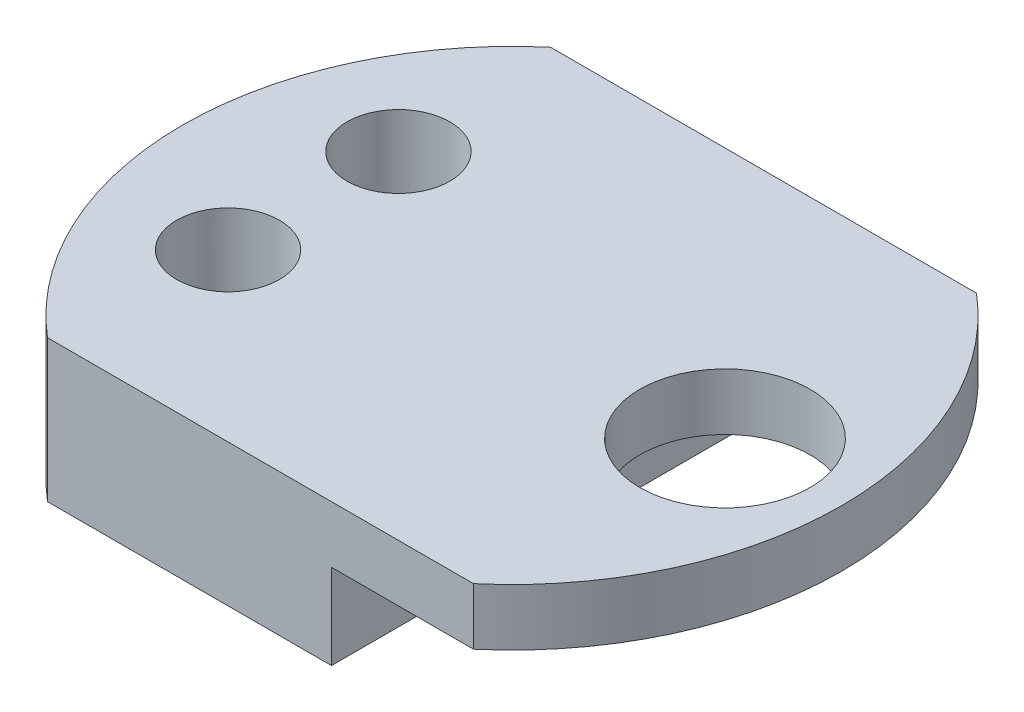
SolidWorks part; units mm, degrees
ref_plane "Front Plane" through (0, 0, 0) normal (0, 0, 1) x (1, 0, 0)
ref_plane "Top Plane" through (0, 0, 0) normal (0, 1, 0) x (1, 0, 0)
ref_plane "Right Plane" through (0, 0, 0) normal (1, 0, 0) x (0, 0, -1)
sketch "Sketch3" plane through (0, 0, 0) normal (0, 1, 0) x (1, 0, 0)
  line L1 (-9.525, 11.25) -> (9.525, 11.25)
  line L3 (-9.525, -11.25) -> (9.525, -11.25)
  line L5 (-9.525, 11.25) -> (9.525, -11.25) construction
  line L6 (-9.525, -11.25) -> (9.525, 11.25) construction
  arc A0 (-9.525, 11.25) -> (-9.525, -11.25) centre (0, 0) ccw
  arc A1 (9.525, -11.25) -> (9.525, 11.25) centre (0, 0) ccw
  point P0 (0, 0)
  dimension "D1" = 22.5
  dimension "D2" = 19.05
extrude "Boss-Extrude2" add sketch "Sketch3" along normal blind 6.35
sketch "Sketch4" plane through (0, 6.35, 0) normal (0, 1, 0) x (1, 0, 0)
  line L0 (-14.7407, 0) -> (14.7407, 0) construction
  line L1 (0, 11.25) -> (0, -11.25) construction
  line L2 (9.525, 11.25) -> (-9.525, 11.25) construction
  line L3 (-9.525, -11.25) -> (9.525, -11.25) construction
  arc A0 (-9.525, 11.25) -> (-9.525, -11.25) centre (0, 0) ccw construction
  arc A1 (9.525, -11.25) -> (9.525, 11.25) centre (0, 0) ccw construction
  circle A2 centre (-8.89, 3.81) radius 2.3
  circle A3 centre (-8.89, -3.81) radius 2.3
  circle A6 centre (9.525, 0) radius 3.81
  dimension "D1" = 4.6
  dimension "D2" = 4.6
  dimension "D4" = 8.89
  dimension "D5" = 7.62
  dimension "D3" = 7.62
extrude "Cut-Extrude1" cut sketch "Sketch4" against normal blind 12.7
sketch "Sketch5" plane through (0, 0, 0) normal (0, -1, 0) x (1, 0, 0)
  line L0 (9.525, -11.25) -> (-9.525, -11.25) construction
  line L1 (9.525, 11.25) -> (3.175, 11.25)
  line L3 (9.525, -11.25) -> (3.175, -11.25)
  line L4 (3.175, 11.25) -> (3.175, -11.25)
  arc A0 (9.525, 11.25) -> (9.525, -11.25) centre (0, 0) cw
  arc A1 (9.525, -11.25) -> (9.525, 11.25) centre (0, 0) ccw construction
  dimension "D1" = 6.35
extrude "Cut-Extrude2" cut sketch "Sketch5" against normal blind 3.81
